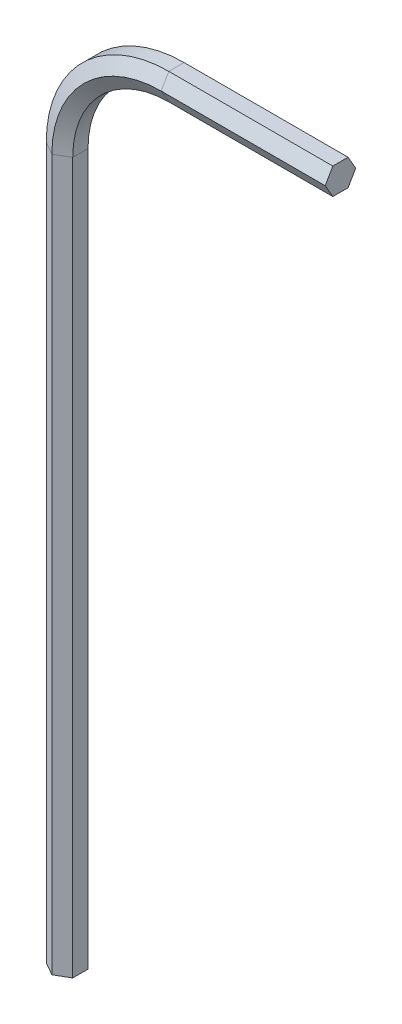
SolidWorks part; units mm, degrees
material "AISI 4340 Steel, normalized"
ref_plane "Front Plane" through (0, 0, 0) normal (0, 0, 1) x (1, 0, 0)
ref_plane "Top Plane" through (0, 0, 0) normal (0, 1, 0) x (1, 0, 0)
ref_plane "Right Plane" through (0, 0, 0) normal (1, 0, 0) x (0, 0, -1)
sketch "Sketch3" plane through (0, 0, 0) normal (0, 1, 0) x (1, 0, 0)
  line L1 (0, 0.866) -> (-0.75, 0.433)
  line L2 (-0.75, 0.433) -> (-0.75, -0.433)
  line L3 (-0.75, -0.433) -> (0, -0.866)
  line L4 (0, -0.866) -> (0.75, -0.433)
  line L5 (0.75, -0.433) -> (0.75, 0.433)
  line L6 (0.75, 0.433) -> (0, 0.866)
  circle A0 centre (0, 0) radius 0.75 construction
  dimension "flats" = 1.5
sketch "Sketch4" plane through (0, 0, 0) normal (0, 0, 1) x (1, 0, 0)
  line L0 (0, 0) -> (0, 40.3)
  line L1 (6.2, 46.5) -> (15.5, 46.5)
  arc A0 (0, 40.3) -> (6.2, 46.5) centre (6.2, 40.3) cw
  point P6 (0, 46.5)
  dimension "fillet" = 6.2
  dimension "L1" = 46.5
  dimension "L2" = 15.5
sweep "Sweep1" add profiles "Sketch3" path "Sketch4"
